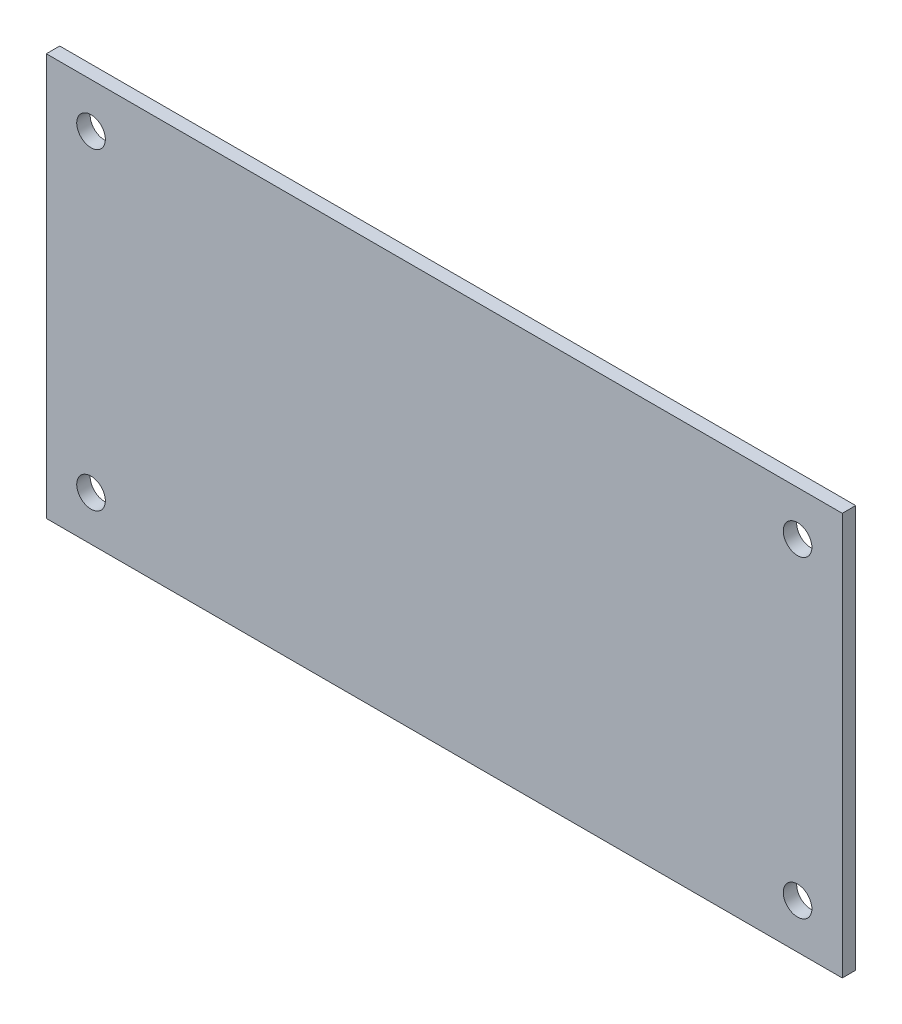
SolidWorks part; units mm, degrees
ref_plane "Front Plane" through (0, 0, 0) normal (0, 0, 1) x (1, 0, 0)
ref_plane "Top Plane" through (0, 0, 0) normal (0, 1, 0) x (1, 0, 0)
ref_plane "Right Plane" through (0, 0, 0) normal (1, 0, 0) x (0, 0, -1)
sketch "Esquisse1" plane through (0, 0, 0) normal (0, 0, 1) x (1, 0, 0)
  line L1 (-44.5, 22.5) -> (44.5, 22.5)
  line L2 (-44.5, 22.5) -> (-44.5, -22.5)
  line L3 (-44.5, -22.5) -> (44.5, -22.5)
  line L4 (44.5, 22.5) -> (44.5, -22.5)
  circle A0 centre (-39.5, 17.5) radius 1.6
  circle A1 centre (-39.5, -17.5) radius 1.6
  circle A2 centre (39.5, -17.5) radius 1.6
  circle A3 centre (39.5, 17.5) radius 1.6
  point P4 (-44.5, 0)
  point P5 (0, -22.5)
  dimension "D3" = 3.2
  dimension "D1" = 89
  dimension "D2" = 45
  dimension "D4" = 5
  dimension "D5" = 5
  dimension "D6" = 5
  dimension "D7" = 5
extrude "Main" add sketch "Esquisse1" along normal blind 1.5
